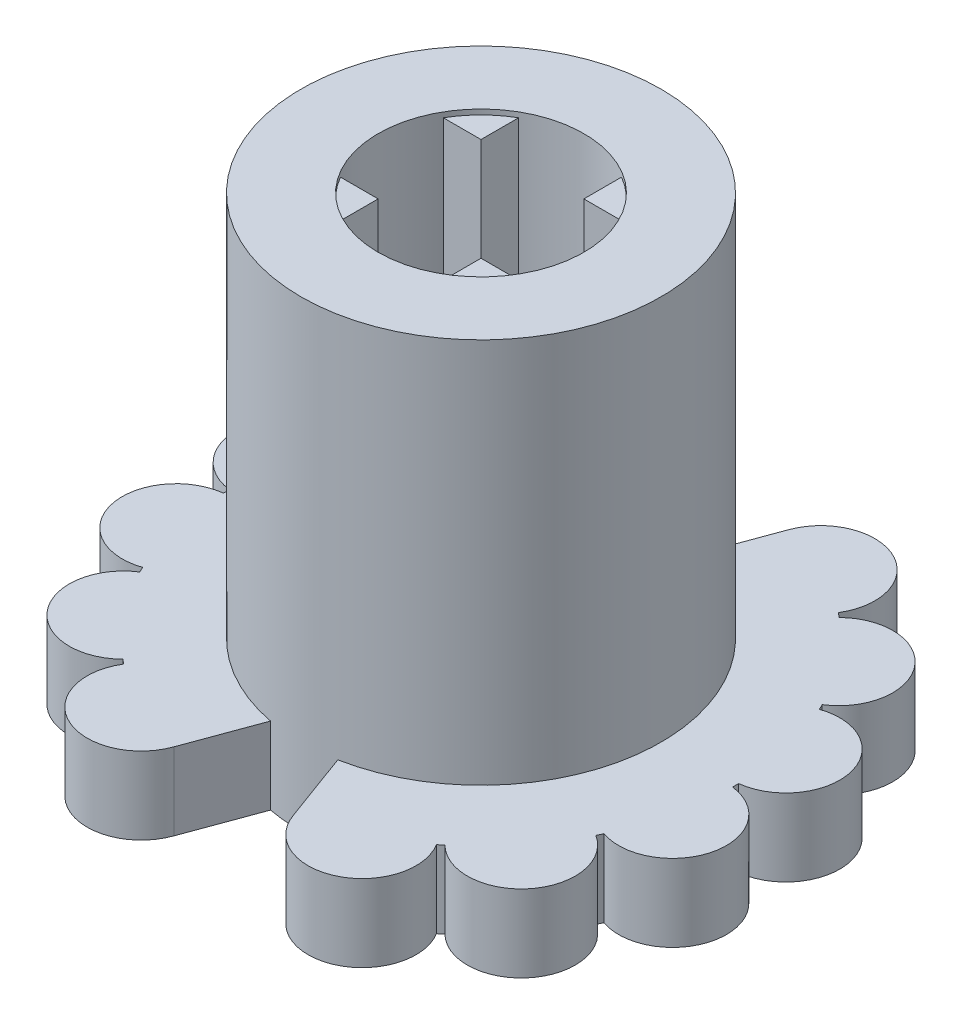
SolidWorks part; units mm, degrees
material "PBT General Purpose"
ref_plane "Front Plane" through (0, 0, 0) normal (0, 0, 1) x (1, 0, 0)
ref_plane "Top Plane" through (0, 0, 0) normal (0, 1, 0) x (1, 0, 0)
ref_plane "Right Plane" through (0, 0, 0) normal (1, 0, 0) x (0, 0, -1)
sketch "Sketch1" plane through (0, 0, 0) normal (0, 1, 0) x (1, 0, 0)
  circle A0 centre (0, 0) radius 6
  circle A1 centre (0, 4.95) radius 1.05
  circle A2 centre (0, 0) radius 4.95
  dimension "D1" = 12
  dimension "D2" = 2.1
extrude "Boss-Extrude1" add sketch "Sketch1" along normal blind 1.5 contours A1 A2 | A2 A1 | A1 A2
pattern_circular "CirPattern1" count 14 over 360 about axis through (0, 0, 0) along (0, 1, 0) of "Boss-Extrude1"
sketch "Sketch2" plane through (0, 1.5, 0) normal (0, 1, 0) x (1, 0, 0)
  line L1 (1, 2) -> (-1, 2)
  line L2 (1, 2) -> (1, -2)
  line L3 (1, -2) -> (-1, -2)
  line L4 (-1, 2) -> (-1, -2)
  line L5 (1, 2) -> (-1, -2) construction
  line L6 (1, -2) -> (-1, 2) construction
  line L7 (-2, 1) -> (2, 1)
  line L8 (-2, 1) -> (-2, -1)
  line L9 (-2, -1) -> (2, -1)
  line L10 (2, 1) -> (2, -1)
  line L11 (-2, 1) -> (2, -1) construction
  line L12 (-2, -1) -> (2, 1) construction
  circle A1 centre (0, 0) radius 2
  circle A2 centre (0, 0) radius 3.5
  point P3 (0, 0)
  dimension "D1" = 2
  dimension "D3" = 7
  dimension "D2" = 4
extrude "Boss-Extrude2" add sketch "Sketch2" along normal blind 7.5 contours A2 A1 L2 L3 L4 L9 L8 L7 L1 L10 | A1 L1 L4 | A1 L2 L1 | A1 L10 L7 | L7 A1 L2 | L4 A1 L7 | A1 L7 L8 | A1 L8 L9 | L9 A1 L4 | A1 L4 L3 | A1 L3 L2 | L2 A1 L9 | A1 L9 L10
sketch "Sketch3" plane through (0, 9, 0) normal (0, 1, 0) x (1, 0, 0)
  circle A0 centre (0, 0) radius 2
  dimension "D1" = 4
extrude "Cut-Extrude1" cut sketch "Sketch3" against normal blind 0.1 contours A0
sketch "Sketch4" plane through (0, 0, 0) normal (0, -1, 0) x (1, 0, 0)
  circle A0 centre (0, 0) radius 1
  dimension "D1" = 2
extrude "Cut-Extrude2" cut sketch "Sketch4" against normal offset from surface (1 mm away) 0.5 up to face at (0, 1.5, 0)
sketch "Sketch5" plane through (0, 9, 0) normal (0, 1, 0) x (1, 0, 0)
  line L0 (-3.0252, 0) -> (3.0252, 0) construction
  line L1 (-1.595, 6) -> (1.595, 6)
  line L2 (-1.595, 6) -> (-0.6538, 3.4384)
  line L4 (1.595, 6) -> (0.6538, 3.4384)
  line L5 (1.595, -6) -> (0.6538, -3.4384)
  line L6 (-1.595, -6) -> (-0.6538, -3.4384)
  line L7 (-1.595, -6) -> (1.595, -6)
  arc A0 (1.0441, 4.8386) -> (-1.0441, 4.8386) centre (0, 4.95) ccw construction
  arc A1 (3.0401, 3.9065) -> (1.1587, 4.8125) centre (2.1477, 4.4598) ccw construction
  arc A2 (-1.1587, 4.8125) -> (-3.0401, 3.9065) centre (-2.1477, 4.4598) ccw construction
  circle A3 centre (0, 0) radius 3.5 construction
  arc A4 (0.6538, 3.4384) -> (-0.6538, 3.4384) centre (0, 0) ccw
  arc A5 (0.6538, -3.4384) -> (-0.6538, -3.4384) centre (0, 0) cw
  point P6 (0, 6)
  point P10 (0, 6)
  dimension "D1" = 2.5616
extrude "Cut-Extrude3" cut sketch "Sketch5" against normal through all both and the other way through all
